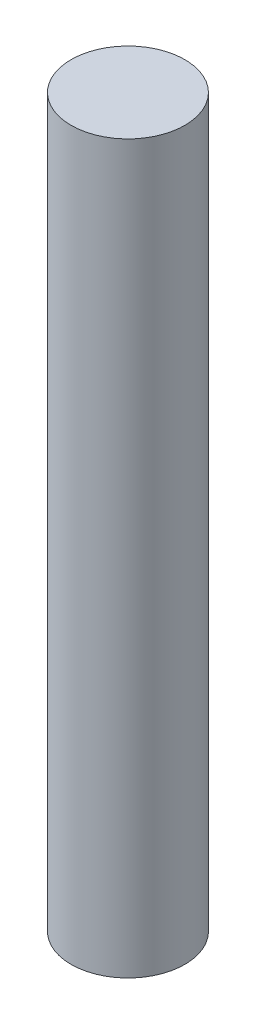
SolidWorks part; units mm, degrees
ref_plane "Front Plane" through (0, 0, 0) normal (0, 0, 1) x (1, 0, 0)
ref_plane "Top Plane" through (0, 0, 0) normal (0, 1, 0) x (1, 0, 0)
ref_plane "Right Plane" through (0, 0, 0) normal (1, 0, 0) x (0, 0, -1)
sketch "Sketch3" plane through (0, 0, 0) normal (0, 1, 0) x (1, 0, 0)
  circle A0 centre (0, 0) radius 0.47
  dimension "D1" = 0.94
extrude "Boss-Extrude1" add sketch "Sketch3" along normal blind 6
